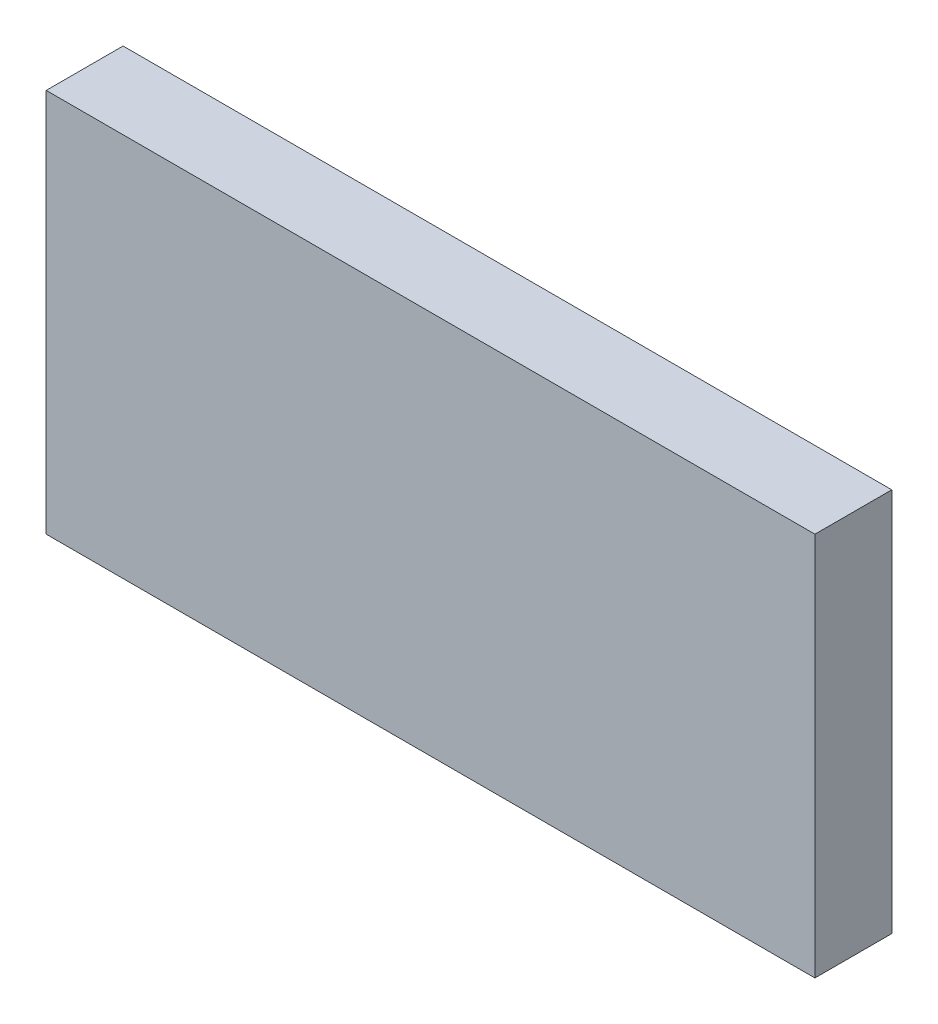
SolidWorks part; units mm, degrees
material "POLYURETHANE (11671)"
ref_plane "Front Plane" through (0, 0, 0) normal (0, 0, 1) x (1, 0, 0)
ref_plane "Top Plane" through (0, 0, 0) normal (0, 1, 0) x (1, 0, 0)
ref_plane "Right Plane" through (0, 0, 0) normal (1, 0, 0) x (0, 0, -1)
sketch "Sketch1" plane through (0, 0, 0) normal (0, 0, 1) x (1, 0, 0)
  line L1 (0, 0) -> (100, 0)
  line L2 (0, 0) -> (0, -50)
  line L3 (0, -50) -> (100, -50)
  line L4 (100, 0) -> (100, -50)
  dimension "D1" = 100
  dimension "D2" = 50
extrude "Boss-Extrude1" add sketch "Sketch1" along normal blind 10
